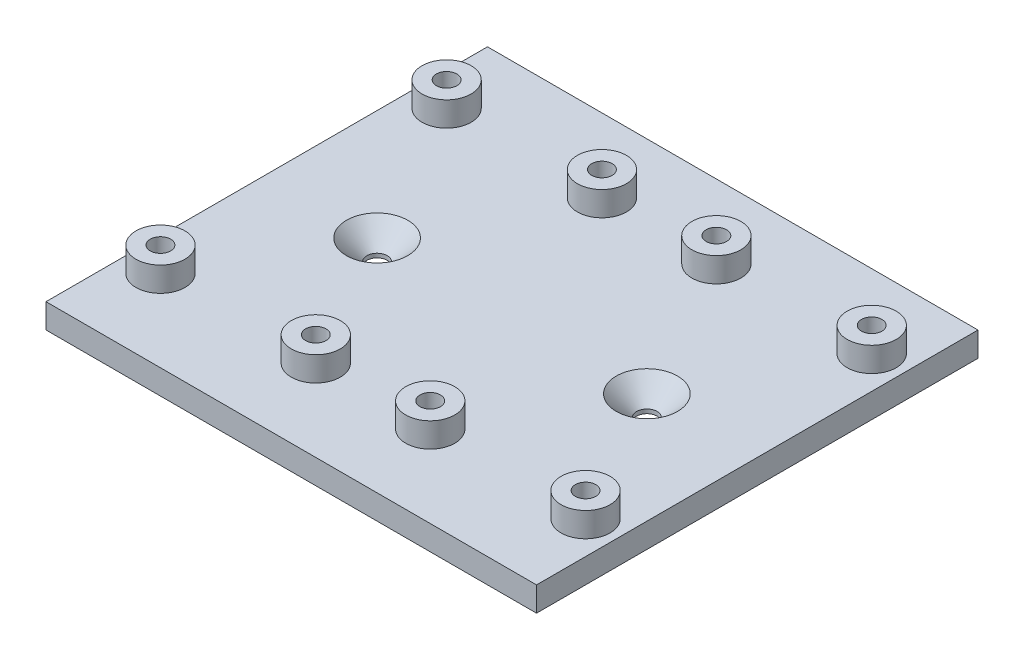
SolidWorks part; units mm, degrees
ref_plane "Спереди" through (0, 0, 0) normal (0, 0, 1) x (1, 0, 0)
ref_plane "Сверху" through (0, 0, 0) normal (0, 1, 0) x (1, 0, 0)
ref_plane "Справа" through (0, 0, 0) normal (1, 0, 0) x (0, 0, -1)
other "Configuration Table"
sketch "Эскиз1" plane through (0, 0, 0) normal (0, 1, 0) x (1, 0, 0)
  line L0 (-1.4657, 26.1615) -> (-1.4657, -27.8385) construction
  line L1 (-31.4657, 26.1615) -> (28.5343, 26.1615)
  line L2 (-31.4657, 26.1615) -> (-31.4657, -27.8385)
  line L3 (-31.4657, -27.8385) -> (28.5343, -27.8385)
  line L4 (28.5343, 26.1615) -> (28.5343, -27.8385)
  dimension "D1" = 60
  dimension "D2" = 54
extrude "Бобышка-Вытянуть1" add sketch "Эскиз1" against normal blind 3 contours L1 L4 L3 L2
sketch "Эскиз3" plane through (0, 0, 0) normal (0, 1, 0) x (1, 0, 0)
  line L0 (-1.4657, 26.1183) -> (-1.4657, -27.8817) construction
  line L1 (-1.4657, 26.1615) -> (-1.4657, -27.8385) construction
  line L3 (-31.4657, 26.1615) -> (28.5343, 26.1615) construction
  line L4 (-31.4657, 26.1615) -> (-31.4657, -27.8385) construction
  line L5 (-27.4657, 17.1615) -> (-8.4657, 17.1615) construction
  line L6 (-17.9657, 17.1615) -> (-17.9657, -17.8385) construction
  line L7 (15.0343, 17.1615) -> (15.0343, -17.8385) construction
  line L8 (24.5343, 17.1615) -> (5.5343, 17.1615) construction
  circle A0 centre (-27.4657, 17.1615) radius 3
  circle A1 centre (-27.4657, 17.1615) radius 1.25
  circle A2 centre (-27.4657, -17.8385) radius 3
  circle A3 centre (-27.4657, -17.8385) radius 1.25
  circle A4 centre (-8.4657, 17.1615) radius 3
  circle A5 centre (-8.4657, 17.1615) radius 1.25
  circle A16 centre (-8.4657, -17.8385) radius 3
  circle A17 centre (-8.4657, -17.8385) radius 1.25
  circle A18 centre (5.5343, -17.8385) radius 1.25
  circle A19 centre (5.5343, -17.8385) radius 3
  circle A20 centre (5.5343, 17.1615) radius 1.25
  circle A21 centre (5.5343, 17.1615) radius 3
  circle A22 centre (24.5343, -17.8385) radius 1.25
  circle A23 centre (24.5343, -17.8385) radius 3
  circle A24 centre (24.5343, 17.1615) radius 1.25
  circle A25 centre (24.5343, 17.1615) radius 3
  point P32 (-8.4657, -17.8385)
  dimension "D1" = 2.5
  dimension "D7" = 2.5
  dimension "D8" = 2.5
  dimension "D9" = 2.5
  dimension "D2" = 9
  dimension "D3" = 4
  dimension "D5" = 35
  dimension "D4" = 19
  dimension "D6" = 19
extrude "Бобышка-Вытянуть2" add sketch "Эскиз3" along normal blind 3
sketch "Эскиз4" plane through (0, 0, 0) normal (0, 1, 0) x (1, 0, 0)
  line L0 (-1.4657, 26.1615) -> (-1.4657, -27.8385) construction
  line L1 (-31.4657, 26.1615) -> (28.5343, 26.1615) construction
  line L2 (-31.4657, -27.8385) -> (28.5343, -27.8385) construction
  line L3 (-27.4657, 17.1615) -> (-8.4657, 17.1615) construction
  line L4 (28.5343, 26.1615) -> (28.5343, -27.8385) construction
  line L5 (28.5343, -0.8385) -> (-31.4657, -0.8385) construction
  line L6 (-31.4657, 26.1615) -> (-31.4657, -27.8385) construction
  line L7 (-17.9657, 17.1615) -> (-17.9657, -0.8385) construction
  circle A0 centre (-17.9657, -0.8385) radius 1.25
  circle A1 centre (15.0343, -0.8385) radius 1.25
  dimension "D1" = 2.5
extrude "Вырез-Вытянуть1" cut sketch "Эскиз4" against normal blind 3
chamfer "Фаска1" distance 2.5 angle 45 2 edges at (15.0343, 0, -0.4115) (-17.9657, 0, 2.0885)
equation "\"D7@Эскиз3\"=\"D1@Эскиз3\""
equation "\"D8@Эскиз3\"=\"D1@Эскиз3\""
equation "\"D9@Эскиз3\"=\"D1@Эскиз3\""
